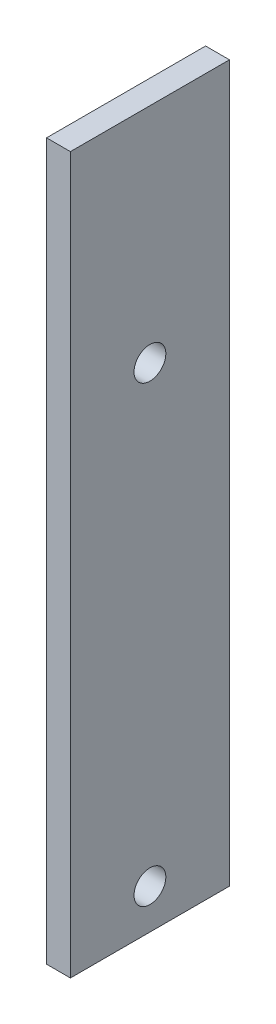
SolidWorks part; units mm, degrees
ref_plane "Front Plane" through (0, 0, 0) normal (0, 0, 1) x (1, 0, 0)
ref_plane "Top Plane" through (0, 0, 0) normal (0, 1, 0) x (1, 0, 0)
ref_plane "Right Plane" through (0, 0, 0) normal (1, 0, 0) x (0, 0, -1)
sketch "Sketch1" plane through (0, 0, 0) normal (1, 0, 0) x (0, 0, -1)
  line L1 (-10, -45) -> (10, -45)
  line L2 (-10, -45) -> (-10, 45)
  line L3 (-10, 45) -> (10, 45)
  line L4 (10, -45) -> (10, 45)
  line L5 (-10, -45) -> (10, 45) construction
  line L6 (-10, 45) -> (10, -45) construction
  point P0 (0, 0)
  dimension "D1" = 90
  dimension "D2" = 20
extrude "Boss-Extrude1" add sketch "Sketch1" along normal blind 3
sketch "Sketch2" plane through (3, 0, 0) normal (1, 0, 0) x (0, 0, -1)
  line L2 (10, 45) -> (-10, 45) construction
  line L3 (10, -45) -> (10, 45) construction
  circle A0 centre (0, 17) radius 2
  circle A1 centre (0, -40) radius 2
  dimension "D1" = 28
  dimension "D3" = 2
  dimension "D2" = 10
extrude "Cut-Extrude1" cut sketch "Sketch2" against normal up to surface (3 mm away) up to face at (0, 0, 0)
